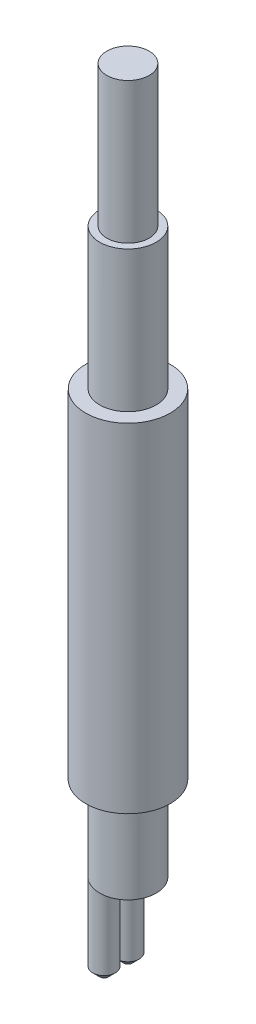
SolidWorks part; units mm, degrees
ref_plane "Ebene vorne" through (0, 0, 0) normal (0, 0, 1) x (1, 0, 0)
ref_plane "Ebene oben" through (0, 0, 0) normal (0, 1, 0) x (1, 0, 0)
ref_plane "Ebene rechts" through (0, 0, 0) normal (1, 0, 0) x (0, 0, -1)
sketch "Skizze1" plane through (0, 0, 0) normal (0, 1, 0) x (1, 0, 0)
  circle A0 centre (0, 0) radius 1
  circle A1 centre (0, 0) radius 0.75
extrude "Aufsatz-Linear austragen1" add sketch "Skizze1" along normal blind 20
sketch "Skizze2" plane through (0, 20, 0) normal (0, 1, 0) x (1, 0, 0)
  circle A0 centre (0, 0) radius 0.75
extrude "Aufsatz-Linear austragen2" add sketch "Skizze2" along normal blind 5 and the other way up to surface (20 mm away) separate body other way up to face at (0, 0, 1)
ref_plane "Ebene1" through (0, 3, 0) normal (0, 1, 0) x (1, 0, 0)
sketch "Skizze3" plane through (0, 3, 0) normal (0, 1, 0) x (1, 0, 0)
  circle A0 centre (0, 0) radius 1.5
extrude "Linear-Austragen-Dünn1" add sketch "Skizze3" along normal blind 12 separate body thin thin type one direction reverse wall 0.5
sketch "Skizze5" plane through (0, 0, 0) normal (0, -1, 0) x (1, 0, 0)
  line L0 (0, 0) -> (-1, 0) construction
  line L1 (0, 0) -> (0, -1) construction
  line L2 (0, 0) -> (-0.4243, -0.4243) construction
  circle A0 centre (0, 0) radius 1 construction
  circle A1 centre (-0.4243, -0.4243) radius 0.4
  circle A2 centre (0, 0) radius 1 construction
  circle A3 centre (-0.4243, 0.4243) radius 0.4
  dimension "D2" = 0.8
  dimension "D1" = 315
extrude "Aufsatz-Linear austragen3" add sketch "Skizze5" along normal blind 3
chamfer "Fase1" distance 0.25 angle 45 2 edges at (-0.4243, -3, -0.8243) (-0.4243, -3, 0.8243)
